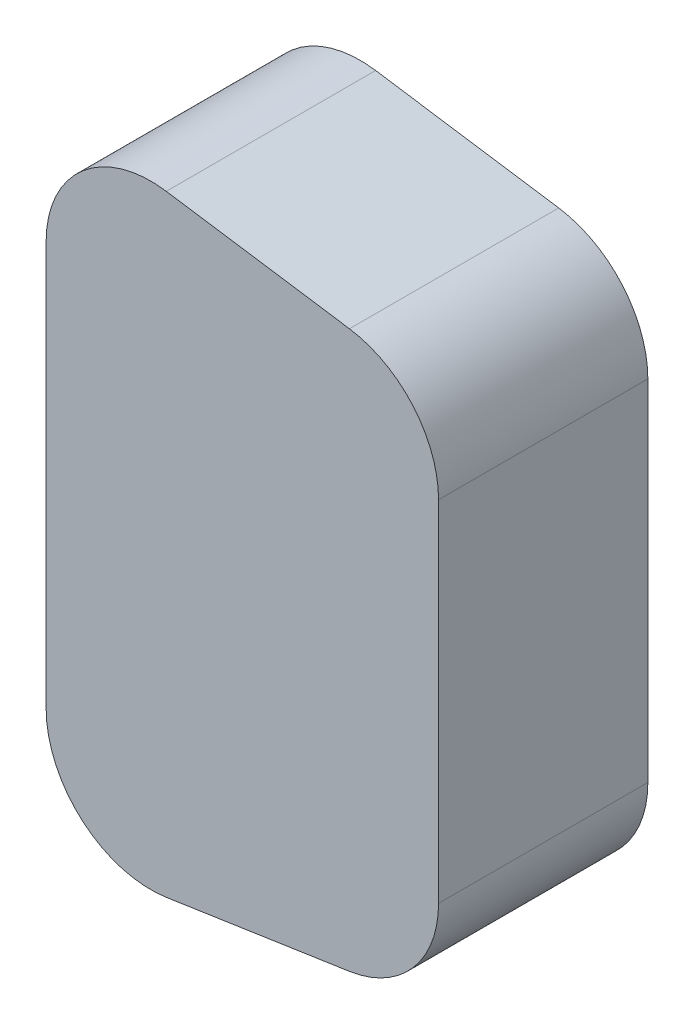
SolidWorks part; units mm, degrees
material "Polyurethane Foam Rigid"
ref_plane "Front Plane" through (0, 0, 0) normal (0, 0, 1) x (1, 0, 0)
ref_plane "Top Plane" through (0, 0, 0) normal (0, 1, 0) x (1, 0, 0)
ref_plane "Right Plane" through (0, 0, 0) normal (1, 0, 0) x (0, 0, -1)
sketch "Sketch1" plane through (0, 0, 0) normal (0, 0, 1) x (1, 0, 0)
  line L0 (0, 72.2334) -> (0, -72.2334) construction
  line L1 (0, 19.3256) -> (0, -19.3256)
  line L2 (-50, 0) -> (50, 0) construction
  line L3 (11.4834, 29.215) -> (28.9834, 26.59)
  line L4 (37.5, -16.7006) -> (37.5, 16.7006)
  line L5 (28.9834, -26.59) -> (11.4834, -29.215)
  arc A0 (28.9834, -26.59) -> (37.5, -16.7006) centre (27.5, -16.7006) ccw
  arc A1 (28.9834, 26.59) -> (37.5, 16.7006) centre (27.5, 16.7006) cw
  arc A2 (0, -19.3256) -> (11.4834, -29.215) centre (10, -19.3256) ccw
  arc A3 (0, 19.3256) -> (11.4834, 29.215) centre (10, 19.3256) cw
  point P13 (37.5, 0)
  point P14 (37.5, -25.3125)
  point P17 (37.5, 25.3125)
  point P20 (0, -30.9375)
  point P23 (0, 30.9375)
  point P24 (26.9612, 0)
  dimension "D4" = 10
  dimension "D5" = 10
  dimension "D1" = 37.5
  dimension "D2" = 61.875
  dimension "D3" = 50.625
extrude "Boss-Extrude1" add sketch "Sketch1" along normal blind 20
sketch "Sketch5" plane through (0, 0, 0) normal (-1, 0, 0) x (0, 0, 1)
  line L0 (10, 19.3256) -> (10, -19.3256) construction
  line L3 (20, 19.3256) -> (0, 19.3256) construction
  line L4 (20, -19.3256) -> (0, -19.3256) construction
  line L5 (5.5, 15.8428) -> (14.5, 15.8428)
  line L6 (5.5, 15.8428) -> (5.5, 17.2971)
  line L7 (5.5, 17.2971) -> (14.5, 17.2971)
  line L8 (14.5, 17.2971) -> (14.5, 15.8428)
  point P8 (10, 15.8428)
  point P9 (10, 17.2971)
  dimension "D1" = 9
extrude "Cut-Extrude4" cut sketch "Sketch5" against normal blind 10
sketch "Sketch6" plane through (0, 17.2971, 0) normal (0, -1, 0) x (1, 0, 0)
  line L0 (0, 10) -> (10.2544, 10) construction
  line L1 (0, 14.5) -> (0, 5.5) construction
  circle A0 centre (2.6449, 10) radius 0.5
extrude "Cut-Extrude5" cut sketch "Sketch6" against normal blind 5
